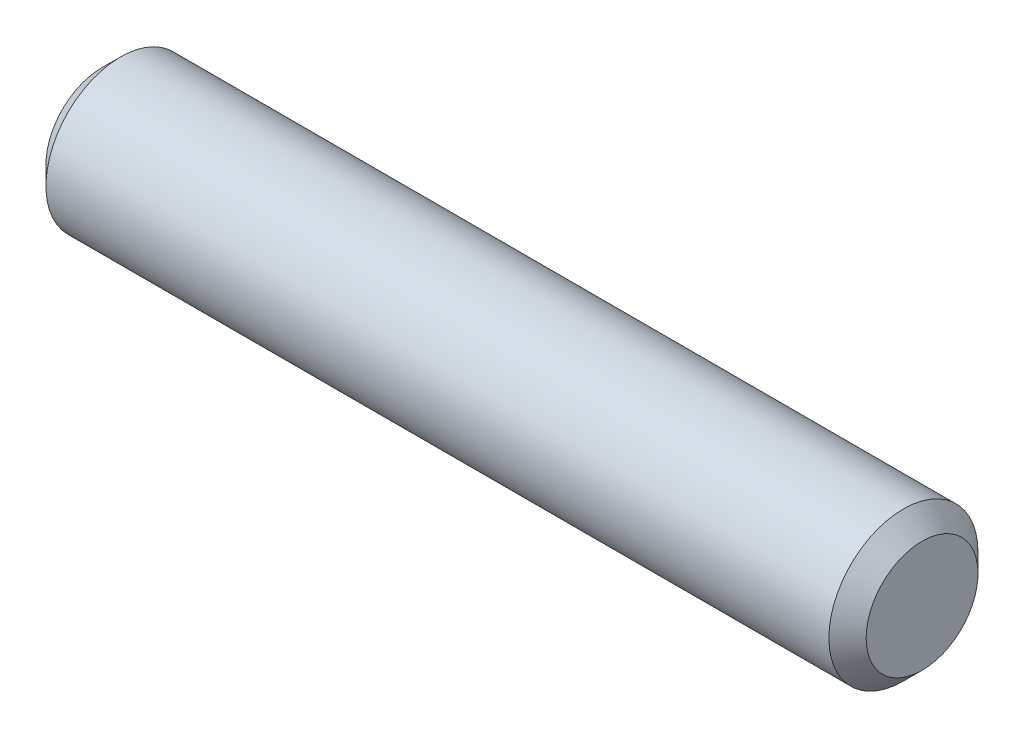
SolidWorks part; units mm, degrees
ref_plane "Front Plane" through (0, 0, 0) normal (0, 0, 1) x (1, 0, 0)
ref_plane "Top Plane" through (0, 0, 0) normal (0, 1, 0) x (1, 0, 0)
ref_plane "Right Plane" through (0, 0, 0) normal (1, 0, 0) x (0, 0, -1)
sketch "Sketch1" plane through (0, 0, 0) normal (0, 0, 1) x (1, 0, 0)
  line L0 (0, 0) -> (22, 0)
  line L1 (22, 0) -> (22, 2)
  line L2 (22, 2) -> (0, 2)
  line L3 (0, 2) -> (0, 0)
  dimension "D1" = 22
  dimension "D2" = 2
revolve "Revolve1" add sketch "Sketch1" angle 360 about L2
chamfer "Chamfer1" distance 0.5 angle 45 2 edges at (0, 4, 0) (22, 4, 0)
